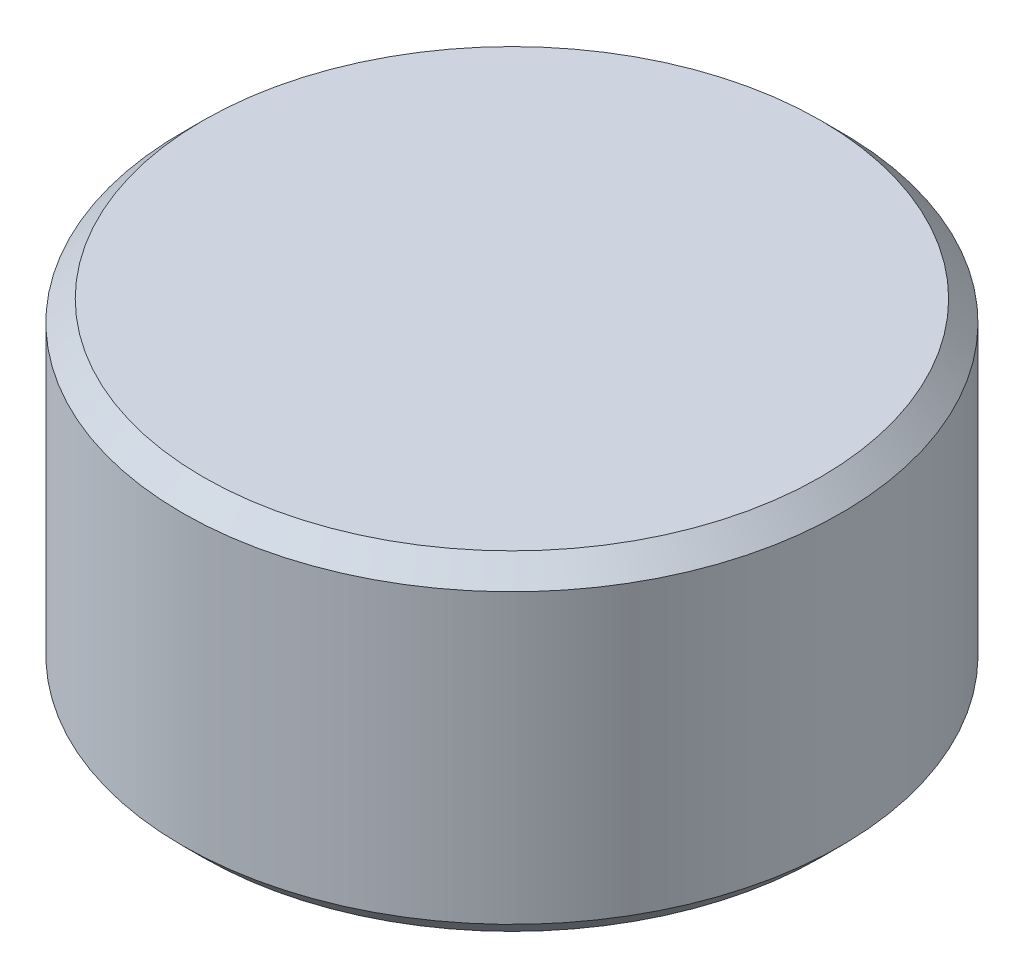
SolidWorks part; units mm, degrees
material "Nickel"
ref_plane "Front Plane" through (0, 0, 0) normal (0, 0, 1) x (1, 0, 0)
ref_plane "Top Plane" through (0, 0, 0) normal (0, 1, 0) x (1, 0, 0)
ref_plane "Right Plane" through (0, 0, 0) normal (1, 0, 0) x (0, 0, -1)
sketch "Sketch1" plane through (0, 0, 0) normal (0, 1, 0) x (1, 0, 0)
  circle A0 centre (0, 0) radius 1.5875
  dimension "D1" = 3.175
extrude "Boss-Extrude1" add sketch "Sketch1" along normal mid plane 1.5875
chamfer "Chamfer1" distance 0.1 angle 45 2 edges at (0, -0.7937, 1.5875) (0, 0.7937, 1.5875)
